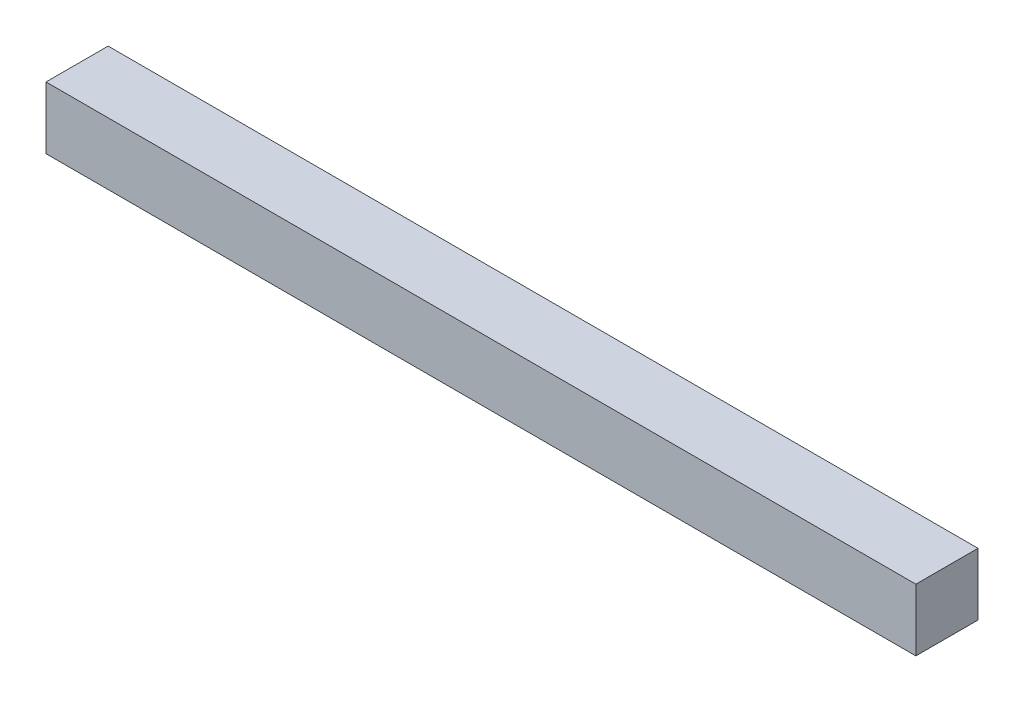
SolidWorks part; units mm, degrees
ref_plane "Front Plane" through (0, 0, 0) normal (0, 0, 1) x (1, 0, 0)
ref_plane "Top Plane" through (0, 0, 0) normal (0, 1, 0) x (1, 0, 0)
ref_plane "Right Plane" through (0, 0, 0) normal (1, 0, 0) x (0, 0, -1)
sketch "Sketch1" plane through (0, 0, 0) normal (0, 1, 0) x (1, 0, 0)
  line L1 (0, 0) -> (70, 0)
  line L2 (0, 0) -> (0, 5)
  line L3 (0, 5) -> (70, 5)
  line L4 (70, 0) -> (70, 5)
  dimension "D1" = 5
  dimension "D2" = 70
extrude "Boss-Extrude1" add sketch "Sketch1" along normal blind 5
